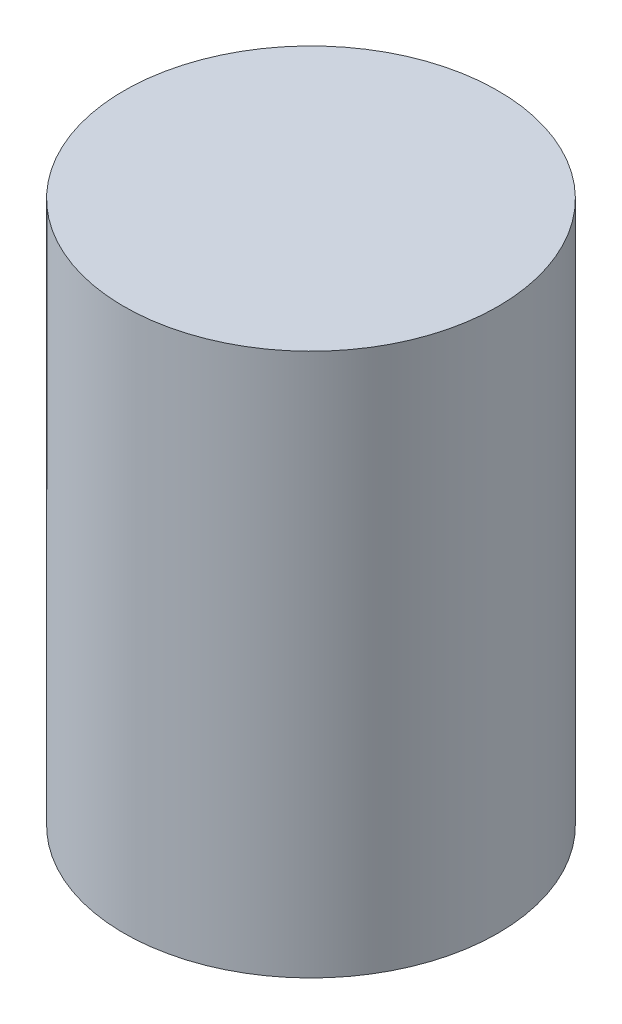
SolidWorks part; units mm, degrees
ref_plane "Front Plane" through (0, 0, 0) normal (0, 0, 1) x (1, 0, 0)
ref_plane "Top Plane" through (0, 0, 0) normal (0, 1, 0) x (1, 0, 0)
ref_plane "Right Plane" through (0, 0, 0) normal (1, 0, 0) x (0, 0, -1)
sketch "Sketch3" plane through (0, 0, 0) normal (0, 0, 1) x (1, 0, 0)
  line L1 (0, 0) -> (35, 0)
  line L2 (0, 0) -> (0, 20)
  line L3 (0, 20) -> (35, 20)
  line L4 (35, 0) -> (35, 20)
  line L5 (35, 0) -> (25, 0)
  line L6 (35, 0) -> (35, 101.6)
  line L7 (35, 101.6) -> (25, 101.6)
  line L8 (25, 0) -> (25, 101.6)
  line L9 (35, 101.6) -> (0, 101.6)
  line L10 (35, 101.6) -> (35, 91.6)
  line L11 (35, 91.6) -> (0, 91.6)
  line L12 (0, 101.6) -> (0, 91.6)
  dimension "D1" = 35
  dimension "D2" = 20
  dimension "D3" = 101.6
  dimension "D4" = 10
  dimension "D5" = 10
  dimension "D6" = 35
ref_axis "Axis1" through (0, -32.02, 0) along (0, 1, 0)
revolve "Revolve2" add sketch "Sketch3" angle 360 about axis through (0, -32.02, 0) along (0, 1, 0)
